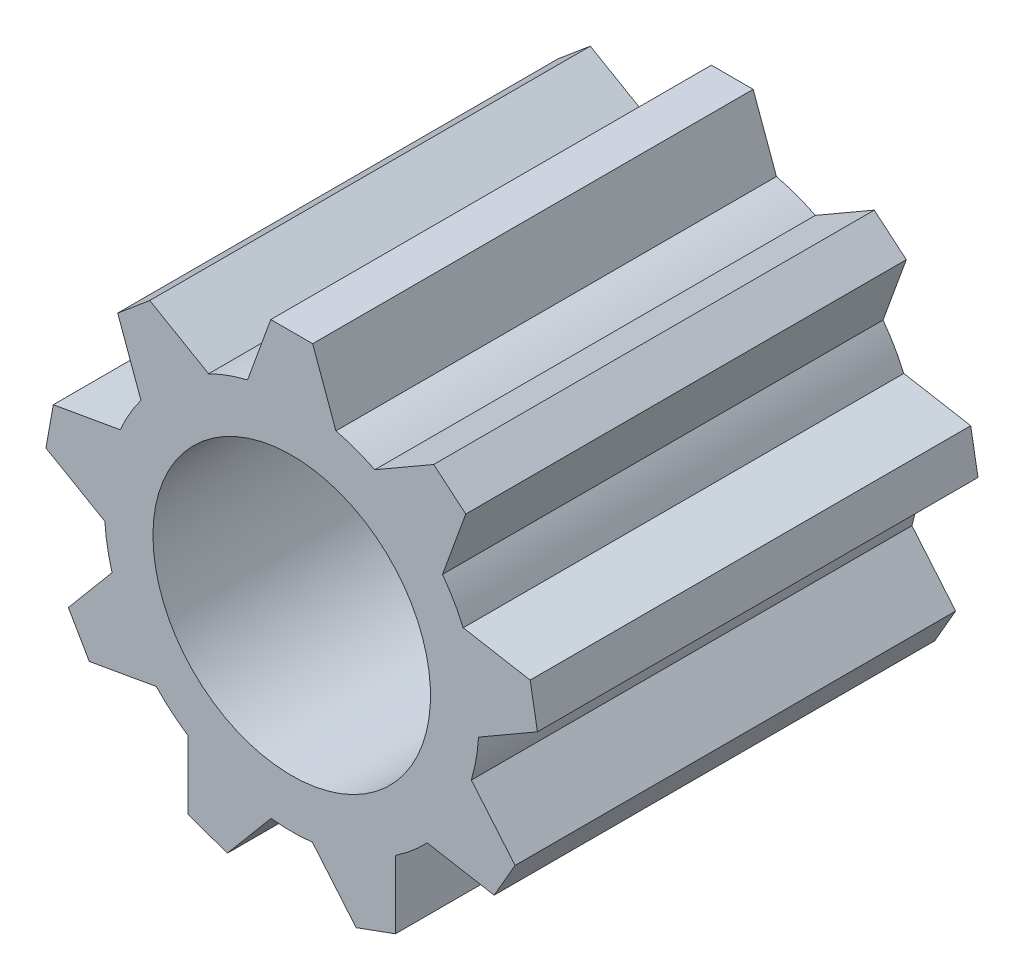
SolidWorks part; units mm, degrees
ref_plane "Front Plane" through (0, 0, 0) normal (0, 0, 1) x (1, 0, 0)
ref_plane "Top Plane" through (0, 0, 0) normal (0, 1, 0) x (1, 0, 0)
ref_plane "Right Plane" through (0, 0, 0) normal (1, 0, 0) x (0, 0, -1)
sketch "Sketch1" plane through (0, 0, 0) normal (0, 0, 1) x (1, 0, 0)
  circle A0 centre (0, 0) radius 4.25
  dimension "D1" = 8.5
extrude "Extrude1" add sketch "Sketch1" along normal blind 10
sketch "Sketch3" plane through (0, 0, 0) normal (0, 0, -1) x (-1, 0, 0)
  circle A0 centre (0, 0) radius 3.15
  dimension "D1" = 6.3
extrude "Extrude2" cut sketch "Sketch3" against normal through all
sketch "Sketch4" plane through (0, 0, 0) normal (0, 0, 1) x (1, 0, 0)
  line L0 (0, 6.8644) -> (0, 0) construction
  line L1 (-0.475, 5.58) -> (0.475, 5.58)
  line L2 (0.475, 5.58) -> (1.0028, 4.13)
  line L3 (1.0028, 4.13) -> (-1.0028, 4.13)
  line L4 (-0.475, 5.58) -> (-1.0028, 4.13)
  circle A1 centre (0, 0) radius 4.25 construction
  point P8 (0, 5.58)
  point P11 (0, 4.13)
  dimension "D1" = 0.95
  dimension "D2" = 70
  dimension "D3" = 1.45
extrude "Extrude3" add sketch "Sketch4" along normal blind 10
pattern_circular "CirPattern1" count 9 over 360 about axis through (0, 0, 0) along (0, 0, 1) of "Extrude3"
